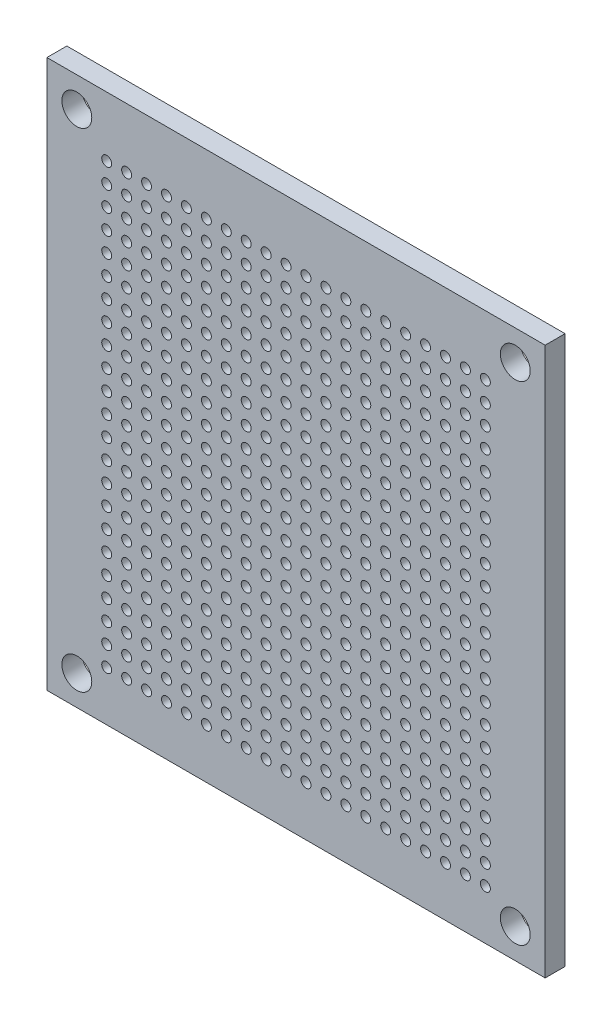
SolidWorks part; units mm, degrees
ref_plane "Plan de face" through (0, 0, 0) normal (0, 0, 1) x (1, 0, 0)
ref_plane "Plan de dessus" through (0, 0, 0) normal (0, 1, 0) x (1, 0, 0)
ref_plane "Plan de droite" through (0, 0, 0) normal (1, 0, 0) x (0, 0, -1)
sketch "Esquisse1" plane through (0, 0, 0) normal (0, 0, 1) x (1, 0, 0)
  line L1 (0, 0) -> (50, 0)
  line L2 (0, 0) -> (0, 55)
  line L3 (0, 55) -> (50, 55)
  line L4 (50, 0) -> (50, 55)
  circle A0 centre (6, 49) radius 0.5
  circle A1 centre (3, 52) radius 1.5
  circle A2 centre (47, 52) radius 1.5
  circle A3 centre (3, 3) radius 1.5
  circle A4 centre (47, 3) radius 1.5
  circle A5 centre (8, 49) radius 0.5
  circle A6 centre (10, 49) radius 0.5
  circle A7 centre (12, 49) radius 0.5
  circle A8 centre (14, 49) radius 0.5
  circle A9 centre (16, 49) radius 0.5
  circle A10 centre (18, 49) radius 0.5
  circle A11 centre (20, 49) radius 0.5
  circle A12 centre (22, 49) radius 0.5
  circle A13 centre (24, 49) radius 0.5
  circle A14 centre (26, 49) radius 0.5
  circle A15 centre (28, 49) radius 0.5
  circle A16 centre (30, 49) radius 0.5
  circle A17 centre (32, 49) radius 0.5
  circle A18 centre (34, 49) radius 0.5
  circle A19 centre (36, 49) radius 0.5
  circle A20 centre (38, 49) radius 0.5
  circle A21 centre (40, 49) radius 0.5
  circle A22 centre (42, 49) radius 0.5
  circle A23 centre (44, 49) radius 0.5
  circle A29 centre (6, 9) radius 0.5
  circle A30 centre (8, 9) radius 0.5
  circle A31 centre (10, 9) radius 0.5
  circle A32 centre (12, 9) radius 0.5
  circle A33 centre (14, 9) radius 0.5
  circle A34 centre (8, 47) radius 0.5
  circle A35 centre (10, 47) radius 0.5
  circle A36 centre (12, 47) radius 0.5
  circle A37 centre (14, 47) radius 0.5
  circle A38 centre (16, 47) radius 0.5
  circle A39 centre (18, 47) radius 0.5
  circle A40 centre (20, 47) radius 0.5
  circle A41 centre (22, 47) radius 0.5
  circle A42 centre (24, 47) radius 0.5
  circle A43 centre (26, 47) radius 0.5
  circle A44 centre (28, 47) radius 0.5
  circle A45 centre (30, 47) radius 0.5
  circle A46 centre (32, 47) radius 0.5
  circle A47 centre (34, 47) radius 0.5
  circle A48 centre (36, 47) radius 0.5
  circle A49 centre (38, 47) radius 0.5
  circle A50 centre (40, 47) radius 0.5
  circle A51 centre (42, 47) radius 0.5
  circle A52 centre (44, 47) radius 0.5
  circle A58 centre (16, 9) radius 0.5
  circle A59 centre (18, 9) radius 0.5
  circle A60 centre (20, 9) radius 0.5
  circle A61 centre (22, 9) radius 0.5
  circle A62 centre (24, 9) radius 0.5
  circle A63 centre (8, 45) radius 0.5
  circle A64 centre (10, 45) radius 0.5
  circle A65 centre (12, 45) radius 0.5
  circle A66 centre (14, 45) radius 0.5
  circle A67 centre (16, 45) radius 0.5
  circle A68 centre (18, 45) radius 0.5
  circle A69 centre (20, 45) radius 0.5
  circle A70 centre (22, 45) radius 0.5
  circle A71 centre (24, 45) radius 0.5
  circle A72 centre (26, 45) radius 0.5
  circle A73 centre (28, 45) radius 0.5
  circle A74 centre (30, 45) radius 0.5
  circle A75 centre (32, 45) radius 0.5
  circle A76 centre (34, 45) radius 0.5
  circle A77 centre (36, 45) radius 0.5
  circle A78 centre (38, 45) radius 0.5
  circle A79 centre (40, 45) radius 0.5
  circle A80 centre (42, 45) radius 0.5
  circle A81 centre (44, 45) radius 0.5
  circle A87 centre (26, 9) radius 0.5
  circle A88 centre (28, 9) radius 0.5
  circle A89 centre (30, 9) radius 0.5
  circle A90 centre (32, 9) radius 0.5
  circle A91 centre (34, 9) radius 0.5
  circle A92 centre (8, 43) radius 0.5
  circle A93 centre (10, 43) radius 0.5
  circle A94 centre (12, 43) radius 0.5
  circle A95 centre (14, 43) radius 0.5
  circle A96 centre (16, 43) radius 0.5
  circle A97 centre (18, 43) radius 0.5
  circle A98 centre (20, 43) radius 0.5
  circle A99 centre (22, 43) radius 0.5
  circle A100 centre (24, 43) radius 0.5
  circle A101 centre (26, 43) radius 0.5
  circle A102 centre (28, 43) radius 0.5
  circle A103 centre (30, 43) radius 0.5
  circle A104 centre (32, 43) radius 0.5
  circle A105 centre (34, 43) radius 0.5
  circle A106 centre (36, 43) radius 0.5
  circle A107 centre (38, 43) radius 0.5
  circle A108 centre (40, 43) radius 0.5
  circle A109 centre (42, 43) radius 0.5
  circle A110 centre (44, 43) radius 0.5
  circle A116 centre (36, 9) radius 0.5
  circle A117 centre (38, 9) radius 0.5
  circle A118 centre (40, 9) radius 0.5
  circle A119 centre (42, 9) radius 0.5
  circle A120 centre (44, 9) radius 0.5
  circle A121 centre (8, 41) radius 0.5
  circle A122 centre (10, 41) radius 0.5
  circle A123 centre (12, 41) radius 0.5
  circle A124 centre (14, 41) radius 0.5
  circle A125 centre (16, 41) radius 0.5
  circle A126 centre (18, 41) radius 0.5
  circle A127 centre (20, 41) radius 0.5
  circle A128 centre (22, 41) radius 0.5
  circle A129 centre (24, 41) radius 0.5
  circle A130 centre (26, 41) radius 0.5
  circle A131 centre (28, 41) radius 0.5
  circle A132 centre (30, 41) radius 0.5
  circle A133 centre (32, 41) radius 0.5
  circle A134 centre (34, 41) radius 0.5
  circle A135 centre (36, 41) radius 0.5
  circle A136 centre (38, 41) radius 0.5
  circle A137 centre (40, 41) radius 0.5
  circle A138 centre (42, 41) radius 0.5
  circle A139 centre (44, 41) radius 0.5
  circle A150 centre (8, 39) radius 0.5
  circle A151 centre (10, 39) radius 0.5
  circle A152 centre (12, 39) radius 0.5
  circle A153 centre (14, 39) radius 0.5
  circle A154 centre (16, 39) radius 0.5
  circle A155 centre (18, 39) radius 0.5
  circle A156 centre (20, 39) radius 0.5
  circle A157 centre (22, 39) radius 0.5
  circle A158 centre (24, 39) radius 0.5
  circle A159 centre (26, 39) radius 0.5
  circle A160 centre (28, 39) radius 0.5
  circle A161 centre (30, 39) radius 0.5
  circle A162 centre (32, 39) radius 0.5
  circle A163 centre (34, 39) radius 0.5
  circle A164 centre (36, 39) radius 0.5
  circle A165 centre (38, 39) radius 0.5
  circle A166 centre (40, 39) radius 0.5
  circle A167 centre (42, 39) radius 0.5
  circle A168 centre (44, 39) radius 0.5
  circle A174 centre (6, 7) radius 0.5
  circle A175 centre (8, 7) radius 0.5
  circle A176 centre (10, 7) radius 0.5
  circle A177 centre (12, 7) radius 0.5
  circle A178 centre (14, 7) radius 0.5
  circle A179 centre (8, 37) radius 0.5
  circle A180 centre (10, 37) radius 0.5
  circle A181 centre (12, 37) radius 0.5
  circle A182 centre (14, 37) radius 0.5
  circle A183 centre (16, 37) radius 0.5
  circle A184 centre (18, 37) radius 0.5
  circle A185 centre (20, 37) radius 0.5
  circle A186 centre (22, 37) radius 0.5
  circle A187 centre (24, 37) radius 0.5
  circle A188 centre (26, 37) radius 0.5
  circle A189 centre (28, 37) radius 0.5
  circle A190 centre (30, 37) radius 0.5
  circle A191 centre (32, 37) radius 0.5
  circle A192 centre (34, 37) radius 0.5
  circle A193 centre (36, 37) radius 0.5
  circle A194 centre (38, 37) radius 0.5
  circle A195 centre (40, 37) radius 0.5
  circle A196 centre (42, 37) radius 0.5
  circle A197 centre (44, 37) radius 0.5
  circle A203 centre (16, 7) radius 0.5
  circle A204 centre (18, 7) radius 0.5
  circle A205 centre (20, 7) radius 0.5
  circle A206 centre (22, 7) radius 0.5
  circle A207 centre (24, 7) radius 0.5
  circle A208 centre (8, 35) radius 0.5
  circle A209 centre (10, 35) radius 0.5
  circle A210 centre (12, 35) radius 0.5
  circle A211 centre (14, 35) radius 0.5
  circle A212 centre (16, 35) radius 0.5
  circle A213 centre (18, 35) radius 0.5
  circle A214 centre (20, 35) radius 0.5
  circle A215 centre (22, 35) radius 0.5
  circle A216 centre (24, 35) radius 0.5
  circle A217 centre (26, 35) radius 0.5
  circle A218 centre (28, 35) radius 0.5
  circle A219 centre (30, 35) radius 0.5
  circle A220 centre (32, 35) radius 0.5
  circle A221 centre (34, 35) radius 0.5
  circle A222 centre (36, 35) radius 0.5
  circle A223 centre (38, 35) radius 0.5
  circle A224 centre (40, 35) radius 0.5
  circle A225 centre (42, 35) radius 0.5
  circle A226 centre (44, 35) radius 0.5
  circle A232 centre (26, 7) radius 0.5
  circle A233 centre (28, 7) radius 0.5
  circle A234 centre (30, 7) radius 0.5
  circle A235 centre (32, 7) radius 0.5
  circle A236 centre (34, 7) radius 0.5
  circle A237 centre (8, 33) radius 0.5
  circle A238 centre (10, 33) radius 0.5
  circle A239 centre (12, 33) radius 0.5
  circle A240 centre (14, 33) radius 0.5
  circle A241 centre (16, 33) radius 0.5
  circle A242 centre (18, 33) radius 0.5
  circle A243 centre (20, 33) radius 0.5
  circle A244 centre (22, 33) radius 0.5
  circle A245 centre (24, 33) radius 0.5
  circle A246 centre (26, 33) radius 0.5
  circle A247 centre (28, 33) radius 0.5
  circle A248 centre (30, 33) radius 0.5
  circle A249 centre (32, 33) radius 0.5
  circle A250 centre (34, 33) radius 0.5
  circle A251 centre (36, 33) radius 0.5
  circle A252 centre (38, 33) radius 0.5
  circle A253 centre (40, 33) radius 0.5
  circle A254 centre (42, 33) radius 0.5
  circle A255 centre (44, 33) radius 0.5
  circle A261 centre (36, 7) radius 0.5
  circle A262 centre (38, 7) radius 0.5
  circle A263 centre (40, 7) radius 0.5
  circle A264 centre (42, 7) radius 0.5
  circle A265 centre (44, 7) radius 0.5
  circle A266 centre (8, 31) radius 0.5
  circle A267 centre (10, 31) radius 0.5
  circle A268 centre (12, 31) radius 0.5
  circle A269 centre (14, 31) radius 0.5
  circle A270 centre (16, 31) radius 0.5
  circle A271 centre (18, 31) radius 0.5
  circle A272 centre (20, 31) radius 0.5
  circle A273 centre (22, 31) radius 0.5
  circle A274 centre (24, 31) radius 0.5
  circle A275 centre (26, 31) radius 0.5
  circle A276 centre (28, 31) radius 0.5
  circle A277 centre (30, 31) radius 0.5
  circle A278 centre (32, 31) radius 0.5
  circle A279 centre (34, 31) radius 0.5
  circle A280 centre (36, 31) radius 0.5
  circle A281 centre (38, 31) radius 0.5
  circle A282 centre (40, 31) radius 0.5
  circle A283 centre (42, 31) radius 0.5
  circle A284 centre (44, 31) radius 0.5
  circle A295 centre (8, 29) radius 0.5
  circle A296 centre (10, 29) radius 0.5
  circle A297 centre (12, 29) radius 0.5
  circle A298 centre (14, 29) radius 0.5
  circle A299 centre (16, 29) radius 0.5
  circle A300 centre (18, 29) radius 0.5
  circle A301 centre (20, 29) radius 0.5
  circle A302 centre (22, 29) radius 0.5
  circle A303 centre (24, 29) radius 0.5
  circle A304 centre (26, 29) radius 0.5
  circle A305 centre (28, 29) radius 0.5
  circle A306 centre (30, 29) radius 0.5
  circle A307 centre (32, 29) radius 0.5
  circle A308 centre (34, 29) radius 0.5
  circle A309 centre (36, 29) radius 0.5
  circle A310 centre (38, 29) radius 0.5
  circle A311 centre (40, 29) radius 0.5
  circle A312 centre (42, 29) radius 0.5
  circle A313 centre (44, 29) radius 0.5
  circle A319 centre (6, 5) radius 0.5
  circle A320 centre (8, 5) radius 0.5
  circle A321 centre (10, 5) radius 0.5
  circle A322 centre (12, 5) radius 0.5
  circle A323 centre (14, 5) radius 0.5
  circle A324 centre (8, 27) radius 0.5
  circle A325 centre (10, 27) radius 0.5
  circle A326 centre (12, 27) radius 0.5
  circle A327 centre (14, 27) radius 0.5
  circle A328 centre (16, 27) radius 0.5
  circle A329 centre (18, 27) radius 0.5
  circle A330 centre (20, 27) radius 0.5
  circle A331 centre (22, 27) radius 0.5
  circle A332 centre (24, 27) radius 0.5
  circle A333 centre (26, 27) radius 0.5
  circle A334 centre (28, 27) radius 0.5
  circle A335 centre (30, 27) radius 0.5
  circle A336 centre (32, 27) radius 0.5
  circle A337 centre (34, 27) radius 0.5
  circle A338 centre (36, 27) radius 0.5
  circle A339 centre (38, 27) radius 0.5
  circle A340 centre (40, 27) radius 0.5
  circle A341 centre (42, 27) radius 0.5
  circle A342 centre (44, 27) radius 0.5
  circle A348 centre (16, 5) radius 0.5
  circle A349 centre (18, 5) radius 0.5
  circle A350 centre (20, 5) radius 0.5
  circle A351 centre (22, 5) radius 0.5
  circle A352 centre (24, 5) radius 0.5
  circle A353 centre (8, 25) radius 0.5
  circle A354 centre (10, 25) radius 0.5
  circle A355 centre (12, 25) radius 0.5
  circle A356 centre (14, 25) radius 0.5
  circle A357 centre (16, 25) radius 0.5
  circle A358 centre (18, 25) radius 0.5
  circle A359 centre (20, 25) radius 0.5
  circle A360 centre (22, 25) radius 0.5
  circle A361 centre (24, 25) radius 0.5
  circle A362 centre (26, 25) radius 0.5
  circle A363 centre (28, 25) radius 0.5
  circle A364 centre (30, 25) radius 0.5
  circle A365 centre (32, 25) radius 0.5
  circle A366 centre (34, 25) radius 0.5
  circle A367 centre (36, 25) radius 0.5
  circle A368 centre (38, 25) radius 0.5
  circle A369 centre (40, 25) radius 0.5
  circle A370 centre (42, 25) radius 0.5
  circle A371 centre (44, 25) radius 0.5
  circle A377 centre (26, 5) radius 0.5
  circle A378 centre (28, 5) radius 0.5
  circle A379 centre (30, 5) radius 0.5
  circle A380 centre (32, 5) radius 0.5
  circle A381 centre (34, 5) radius 0.5
  circle A382 centre (8, 23) radius 0.5
  circle A383 centre (10, 23) radius 0.5
  circle A384 centre (12, 23) radius 0.5
  circle A385 centre (14, 23) radius 0.5
  circle A386 centre (16, 23) radius 0.5
  circle A387 centre (18, 23) radius 0.5
  circle A388 centre (20, 23) radius 0.5
  circle A389 centre (22, 23) radius 0.5
  circle A390 centre (24, 23) radius 0.5
  circle A391 centre (26, 23) radius 0.5
  circle A392 centre (28, 23) radius 0.5
  circle A393 centre (30, 23) radius 0.5
  circle A394 centre (32, 23) radius 0.5
  circle A395 centre (34, 23) radius 0.5
  circle A396 centre (36, 23) radius 0.5
  circle A397 centre (38, 23) radius 0.5
  circle A398 centre (40, 23) radius 0.5
  circle A399 centre (42, 23) radius 0.5
  circle A400 centre (44, 23) radius 0.5
  circle A406 centre (36, 5) radius 0.5
  circle A407 centre (38, 5) radius 0.5
  circle A408 centre (40, 5) radius 0.5
  circle A409 centre (42, 5) radius 0.5
  circle A410 centre (44, 5) radius 0.5
  circle A411 centre (8, 21) radius 0.5
  circle A412 centre (10, 21) radius 0.5
  circle A413 centre (12, 21) radius 0.5
  circle A414 centre (14, 21) radius 0.5
  circle A415 centre (16, 21) radius 0.5
  circle A416 centre (18, 21) radius 0.5
  circle A417 centre (20, 21) radius 0.5
  circle A418 centre (22, 21) radius 0.5
  circle A419 centre (24, 21) radius 0.5
  circle A420 centre (26, 21) radius 0.5
  circle A421 centre (28, 21) radius 0.5
  circle A422 centre (30, 21) radius 0.5
  circle A423 centre (32, 21) radius 0.5
  circle A424 centre (34, 21) radius 0.5
  circle A425 centre (36, 21) radius 0.5
  circle A426 centre (38, 21) radius 0.5
  circle A427 centre (40, 21) radius 0.5
  circle A428 centre (42, 21) radius 0.5
  circle A429 centre (44, 21) radius 0.5
  circle A440 centre (8, 19) radius 0.5
  circle A441 centre (10, 19) radius 0.5
  circle A442 centre (12, 19) radius 0.5
  circle A443 centre (14, 19) radius 0.5
  circle A444 centre (16, 19) radius 0.5
  circle A445 centre (18, 19) radius 0.5
  circle A446 centre (20, 19) radius 0.5
  circle A447 centre (22, 19) radius 0.5
  circle A448 centre (24, 19) radius 0.5
  circle A449 centre (26, 19) radius 0.5
  circle A450 centre (28, 19) radius 0.5
  circle A451 centre (30, 19) radius 0.5
  circle A452 centre (32, 19) radius 0.5
  circle A453 centre (34, 19) radius 0.5
  circle A454 centre (36, 19) radius 0.5
  circle A455 centre (38, 19) radius 0.5
  circle A456 centre (40, 19) radius 0.5
  circle A457 centre (42, 19) radius 0.5
  circle A458 centre (44, 19) radius 0.5
  circle A469 centre (8, 17) radius 0.5
  circle A470 centre (10, 17) radius 0.5
  circle A471 centre (12, 17) radius 0.5
  circle A472 centre (14, 17) radius 0.5
  circle A473 centre (16, 17) radius 0.5
  circle A474 centre (18, 17) radius 0.5
  circle A475 centre (20, 17) radius 0.5
  circle A476 centre (22, 17) radius 0.5
  circle A477 centre (24, 17) radius 0.5
  circle A478 centre (26, 17) radius 0.5
  circle A479 centre (28, 17) radius 0.5
  circle A480 centre (30, 17) radius 0.5
  circle A481 centre (32, 17) radius 0.5
  circle A482 centre (34, 17) radius 0.5
  circle A483 centre (36, 17) radius 0.5
  circle A484 centre (38, 17) radius 0.5
  circle A485 centre (40, 17) radius 0.5
  circle A486 centre (42, 17) radius 0.5
  circle A487 centre (44, 17) radius 0.5
  circle A498 centre (8, 15) radius 0.5
  circle A499 centre (10, 15) radius 0.5
  circle A500 centre (12, 15) radius 0.5
  circle A501 centre (14, 15) radius 0.5
  circle A502 centre (16, 15) radius 0.5
  circle A503 centre (18, 15) radius 0.5
  circle A504 centre (20, 15) radius 0.5
  circle A505 centre (22, 15) radius 0.5
  circle A506 centre (24, 15) radius 0.5
  circle A507 centre (26, 15) radius 0.5
  circle A508 centre (28, 15) radius 0.5
  circle A509 centre (30, 15) radius 0.5
  circle A510 centre (32, 15) radius 0.5
  circle A511 centre (34, 15) radius 0.5
  circle A512 centre (36, 15) radius 0.5
  circle A513 centre (38, 15) radius 0.5
  circle A514 centre (40, 15) radius 0.5
  circle A515 centre (42, 15) radius 0.5
  circle A516 centre (44, 15) radius 0.5
  circle A527 centre (6, 47) radius 0.5
  circle A528 centre (6, 45) radius 0.5
  circle A529 centre (6, 43) radius 0.5
  circle A530 centre (6, 41) radius 0.5
  circle A531 centre (6, 39) radius 0.5
  circle A532 centre (6, 37) radius 0.5
  circle A533 centre (6, 35) radius 0.5
  circle A534 centre (6, 33) radius 0.5
  circle A535 centre (6, 31) radius 0.5
  circle A536 centre (6, 29) radius 0.5
  circle A537 centre (6, 27) radius 0.5
  circle A538 centre (6, 25) radius 0.5
  circle A539 centre (6, 23) radius 0.5
  circle A540 centre (6, 21) radius 0.5
  circle A541 centre (6, 19) radius 0.5
  circle A542 centre (6, 17) radius 0.5
  circle A543 centre (6, 15) radius 0.5
  circle A544 centre (6, 13) radius 0.5
  circle A545 centre (8, 13) radius 0.5
  circle A546 centre (10, 13) radius 0.5
  circle A547 centre (12, 13) radius 0.5
  circle A548 centre (14, 13) radius 0.5
  circle A549 centre (16, 13) radius 0.5
  circle A550 centre (18, 13) radius 0.5
  circle A551 centre (20, 13) radius 0.5
  circle A552 centre (22, 13) radius 0.5
  circle A553 centre (24, 13) radius 0.5
  circle A554 centre (26, 13) radius 0.5
  circle A555 centre (28, 13) radius 0.5
  circle A556 centre (30, 13) radius 0.5
  circle A557 centre (32, 13) radius 0.5
  circle A558 centre (34, 13) radius 0.5
  circle A559 centre (36, 13) radius 0.5
  circle A560 centre (38, 13) radius 0.5
  circle A561 centre (40, 13) radius 0.5
  circle A562 centre (42, 13) radius 0.5
  circle A563 centre (44, 13) radius 0.5
  circle A574 centre (6, 11) radius 0.5
  circle A575 centre (8, 11) radius 0.5
  circle A576 centre (10, 11) radius 0.5
  circle A577 centre (12, 11) radius 0.5
  circle A578 centre (14, 11) radius 0.5
  circle A579 centre (16, 11) radius 0.5
  circle A580 centre (18, 11) radius 0.5
  circle A581 centre (20, 11) radius 0.5
  circle A582 centre (22, 11) radius 0.5
  circle A583 centre (24, 11) radius 0.5
  circle A584 centre (26, 11) radius 0.5
  circle A585 centre (28, 11) radius 0.5
  circle A586 centre (30, 11) radius 0.5
  circle A587 centre (32, 11) radius 0.5
  circle A588 centre (34, 11) radius 0.5
  circle A589 centre (36, 11) radius 0.5
  circle A590 centre (38, 11) radius 0.5
  circle A591 centre (40, 11) radius 0.5
  circle A592 centre (42, 11) radius 0.5
  circle A593 centre (44, 11) radius 0.5
  dimension "D3" = 1
  dimension "D6" = 3
  dimension "D7" = 3
  dimension "D9" = 3
  dimension "D12" = 3
  dimension "D1" = 50
  dimension "D2" = 55
  dimension "D4" = 3
  dimension "D5" = 3
  dimension "D8" = 3
  dimension "D10" = 3
  dimension "D11" = 3
  dimension "D13" = 6
  dimension "D14" = 6
  dimension "D15" = 20
  dimension "D16" = 23
extrude "Boss.-Extru.1" add sketch "Esquisse1" along normal blind 2
